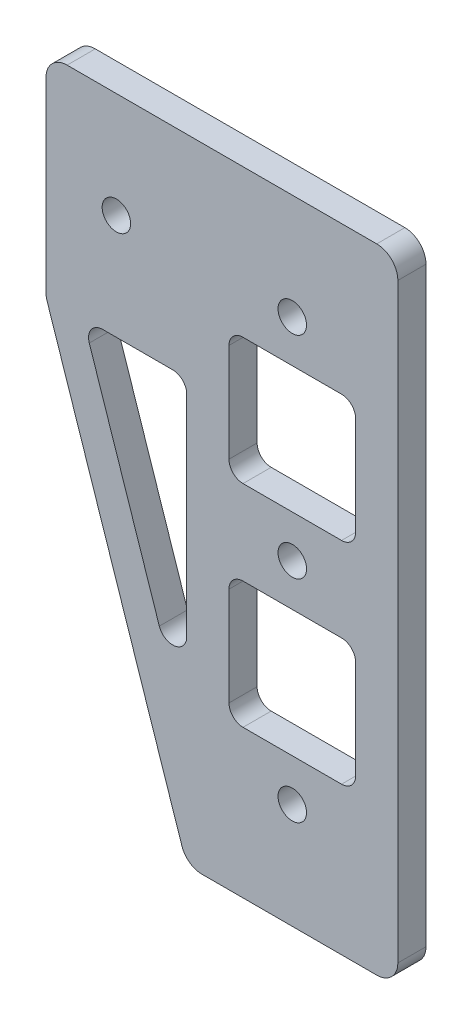
SolidWorks part; units mm, degrees
material "Thornel Mat VMA"
ref_plane "前视基准面" through (0, 0, 0) normal (0, 0, 1) x (1, 0, 0)
ref_plane "上视基准面" through (0, 0, 0) normal (0, 1, 0) x (1, 0, 0)
ref_plane "右视基准面" through (0, 0, 0) normal (1, 0, 0) x (0, 0, -1)
other "Configuration Table"
sketch "草图1" plane through (0, 0, 0) normal (0, 0, 1) x (1, 0, 0)
  line L0 (0, 0) -> (0, -90)
  line L5 (0, -90) -> (-30, -90)
  line L6 (-30, -90) -> (-50, -30)
  line L11 (-50, -30) -> (-50, 0)
  line L12 (-50, 0) -> (0, 0)
  dimension "D1" = 30
  dimension "D2" = 30
  dimension "D3" = 90
  dimension "D4" = 50
extrude "凸台-拉伸1" add sketch "草图1" along normal blind 4
sketch "草图2" plane through (0, 0, 4) normal (0, 0, 1) x (1, 0, 0)
  line L0 (-50, 0) -> (0, 0) construction
  line L1 (0, 0) -> (0, -90) construction
  line L2 (0, -90) -> (-30, -90) construction
  circle A1 centre (-15, -75) radius 2.025
  circle A2 centre (-15, -45) radius 2.025
  circle A4 centre (-15, -15) radius 2.025
  circle A5 centre (-40, -15) radius 2.025
  dimension "D1" = 4.05
  dimension "D2" = 15
  dimension "D3" = 25
  dimension "D4" = 15
  dimension "D5" = 15
  dimension "D6" = 30
extrude "切除-拉伸1" cut sketch "草图2" against normal through all
sketch "草图3" plane through (0, 0, 4) normal (0, 0, 1) x (1, 0, 0)
  line L0 (-44.7295, -30) -> (-30, -30)
  line L1 (-24, -39) -> (-6, -39)
  line L2 (-24, -39) -> (-24, -21)
  line L3 (-24, -21) -> (-6, -21)
  line L4 (-6, -39) -> (-6, -21)
  line L5 (-24, -39) -> (-6, -21) construction
  line L6 (-24, -21) -> (-6, -39) construction
  line L7 (-24, -69) -> (-6, -69)
  line L8 (-24, -69) -> (-24, -51)
  line L9 (-24, -51) -> (-6, -51)
  line L10 (-6, -69) -> (-6, -51)
  line L11 (-24, -69) -> (-6, -51) construction
  line L12 (-24, -51) -> (-6, -69) construction
  line L13 (-30, -30) -> (-30, -74.1886)
  line L14 (-30, -74.1886) -> (-44.7295, -30)
  line L15 (-30, -90) -> (-50, -30) construction
  line L16 (-15, -15) -> (-15, -45) construction
  line L17 (-15, -45) -> (-15, -75) construction
  line L18 (0, 0) -> (0, -90) construction
  point P0 (-15, -30)
  point P5 (-15, -60)
  dimension "D1" = 5
  dimension "D2" = 18
  dimension "D3" = 30
  dimension "D5" = 18
extrude "切除-拉伸2" cut sketch "草图3" against normal through all
fillet "圆角1" radius 2 11 edges at (-24, -39, 2) (-24, -21, 2) (-6, -21, 2) (-6, -39, 2) (-24, -69, 2) (-24, -51, 2) (-6, -51, 2) (-6, -69, 2) (-30, -74.1886, 2) (-44.7295, -30, 2) (-30, -30, 2)
fillet "圆角2" radius 3 5 edges at (0, -90, 2) (-30, -90, 2) (-50, -30, 2) (0, 0, 2) (-50, 0, 2)
